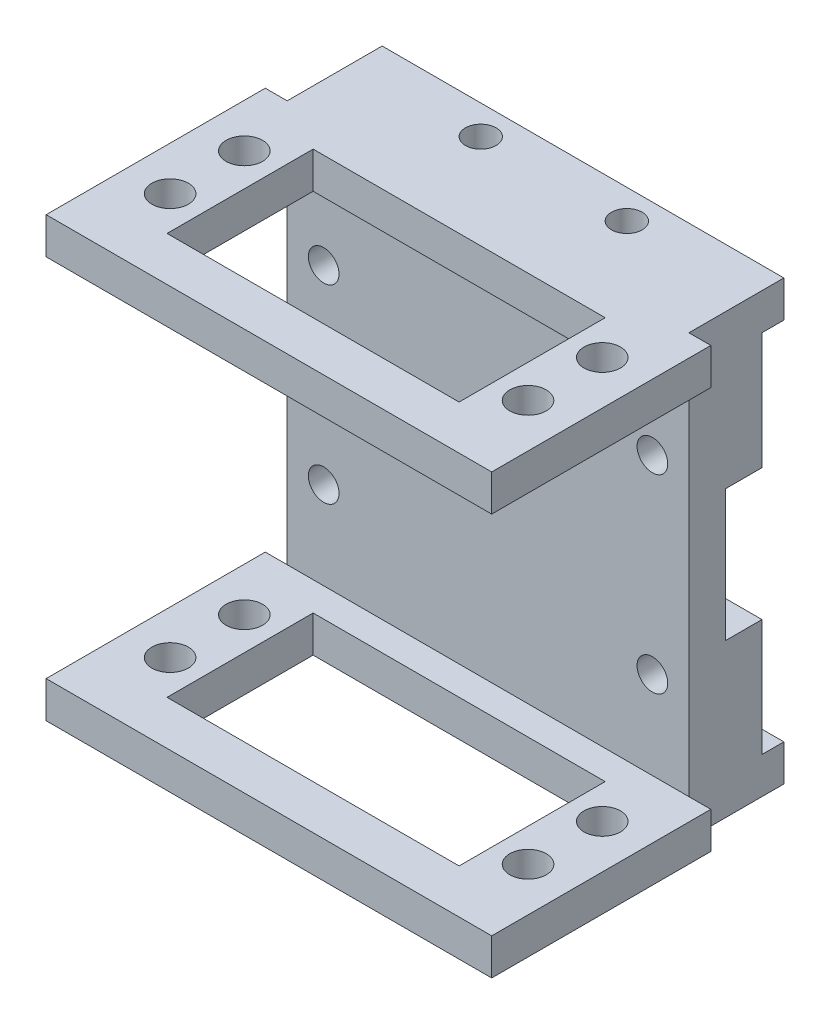
SolidWorks part; units mm, degrees
ref_plane "Front Plane" through (0, 0, 0) normal (0, 0, 1) x (1, 0, 0)
ref_plane "Top Plane" through (0, 0, 0) normal (0, 1, 0) x (1, 0, 0)
ref_plane "Right Plane" through (0, 0, 0) normal (1, 0, 0) x (0, 0, -1)
sketch "Sketch1" plane through (0, 0, 0) normal (0, 0, 1) x (1, 0, 0)
  line L0 (23.841, 9.1341) -> (28.841, 9.1341)
  line L1 (19.841, 25.1341) -> (19.841, 13.1341)
  line L2 (-26.159, 9.1341) -> (-21.159, 9.1341)
  line L3 (-17.159, 13.1341) -> (-17.159, 25.1341)
  line L4 (28.841, -8.8659) -> (23.841, -8.8659)
  line L5 (19.841, -12.8659) -> (19.841, -24.8659)
  line L6 (-17.159, -24.8659) -> (-17.159, -12.8659)
  line L7 (-21.159, -8.8659) -> (-26.159, -8.8659)
  line L8 (-17.159, -24.8659) -> (-26.159, -24.8659)
  line L9 (-26.159, -8.8659) -> (-26.159, -24.8659)
  line L10 (28.841, -24.8659) -> (28.841, -8.8659)
  line L11 (28.841, -24.8659) -> (19.841, -24.8659)
  line L12 (28.841, 9.1341) -> (28.841, 25.1341)
  line L13 (19.841, 25.1341) -> (28.841, 25.1341)
  line L14 (-26.159, 25.1341) -> (-17.159, 25.1341)
  line L15 (-26.159, 25.1341) -> (-26.159, 9.1341)
  arc A0 (19.841, 13.1341) -> (23.841, 9.1341) centre (23.841, 13.1341) ccw
  arc A1 (-21.159, 9.1341) -> (-17.159, 13.1341) centre (-21.159, 13.1341) ccw
  arc A2 (23.841, -8.8659) -> (19.841, -12.8659) centre (23.841, -12.8659) ccw
  arc A3 (-17.159, -12.8659) -> (-21.159, -8.8659) centre (-21.159, -12.8659) ccw
extrude "Boss-Extrude1" add sketch "Sketch1" along normal blind 5
sketch "Sketch2" plane through (0, 0, 5) normal (0, 0, 1) x (1, 0, 0)
  line L1 (-26.159, 25.1341) -> (28.841, 25.1341)
  line L2 (-26.159, 25.1341) -> (-26.159, -24.8659)
  line L3 (-26.159, -24.8659) -> (28.841, -24.8659)
  line L4 (28.841, 25.1341) -> (28.841, -24.8659)
  line L5 (-26.159, 25.1341) -> (28.841, -24.8659) construction
  line L6 (-26.159, -24.8659) -> (28.841, 25.1341) construction
  point P4 (1.341, 0.1341)
extrude "Boss-Extrude2" add sketch "Sketch2" along normal blind 5
sketch "Sketch3" plane through (0, 25.1341, 0) normal (0, 1, 0) x (1, 0, 0)
  line L0 (28.841, 0) -> (28.841, 12) construction
  line L1 (-26.159, -10) -> (28.841, -10)
  line L2 (-26.159, -10) -> (-26.159, 3)
  line L3 (-26.159, 3) -> (28.841, 3)
  line L4 (28.841, -10) -> (28.841, 3)
  line L5 (-26.159, -10) -> (28.841, 3) construction
  line L6 (-26.159, 3) -> (28.841, -10) construction
  line L7 (-5.159, 3) -> (-12.159, 3) construction
  circle A0 centre (-8.659, -1) radius 2.1
  circle A1 centre (11.341, -1) radius 2.1
  point P4 (1.341, -3.5)
extrude "Boss-Extrude3" add sketch "Sketch3" along normal blind 5
ref_plane "Plane1" through (0, 0.1341, 0) normal (0, -1, 0) x (-1, 0, 0)
mirror "Mirror1" about plane through (0, 0.1341, 0) normal (0, -1, 0) of "Boss-Extrude3"
sketch "Sketch4" plane through (0, 30.1341, 0) normal (0, 1, 0) x (1, 0, 0)
  line L0 (-26.159, 3) -> (-26.159, -10) construction
  line L1 (-29.159, -10) -> (31.841, -10)
  line L2 (-29.159, -10) -> (-29.159, -40)
  line L3 (-29.159, -40) -> (31.841, -40)
  line L4 (31.841, -10) -> (31.841, -40)
  line L5 (-29.159, -10) -> (31.841, -40) construction
  line L6 (-29.159, -40) -> (31.841, -10) construction
  line L7 (28.841, -10) -> (28.841, 3) construction
  point P4 (1.341, -25)
  dimension "D1" = 30
  dimension "D2" = 3
  dimension "D3" = 3
extrude "Boss-Extrude4" add sketch "Sketch4" against normal blind 5
mirror "Mirror2" about plane through (0, 0.1341, 0) normal (0, -1, 0) of "Boss-Extrude4"
sketch "Sketch5" plane through (0, 25.1341, 0) normal (0, -1, 0) x (1, 0, 0)
  line L0 (-24.709, 33.9459) -> (-17.659, 33.9459) construction
  line L1 (-18.659, 33.9459) -> (21.3242, 33.9459)
  line L2 (-18.659, 33.9459) -> (-18.659, 13.9459)
  line L3 (-18.659, 13.9459) -> (21.3242, 13.9459)
  line L4 (21.3242, 33.9459) -> (21.3242, 13.9459)
  line L5 (-18.659, 33.9459) -> (21.3242, 13.9459) construction
  line L6 (-18.659, 13.9459) -> (21.3242, 33.9459) construction
  line L7 (27.391, 13.9459) -> (20.341, 13.9459) construction
  circle A0 centre (-23.159, 29.0259) radius 2.5
  circle A1 centre (-23.159, 18.8659) radius 2.5
  circle A2 centre (25.841, 29.0259) radius 2.5
  circle A3 centre (25.841, 18.8659) radius 2.5
  point P16 (1.3326, 23.9459)
extrude "Cut-Extrude3" cut sketch "Sketch5" against normal blind 5
sketch "Sketch7" plane through (0, 0, 10) normal (0, 0, 1) x (1, 0, 0)
  circle A0 centre (23.841, -12.8659) radius 2.1
  circle A1 centre (-21.159, -12.8659) radius 2.1
  circle A2 centre (23.841, 13.1341) radius 2.1
  circle A3 centre (-21.159, 13.1341) radius 2.1
extrude "Cut-Extrude4" cut sketch "Sketch7" against normal through all
mirror "Mirror3" about plane through (0, 0.1341, 0) normal (0, -1, 0) of "Cut-Extrude3"
